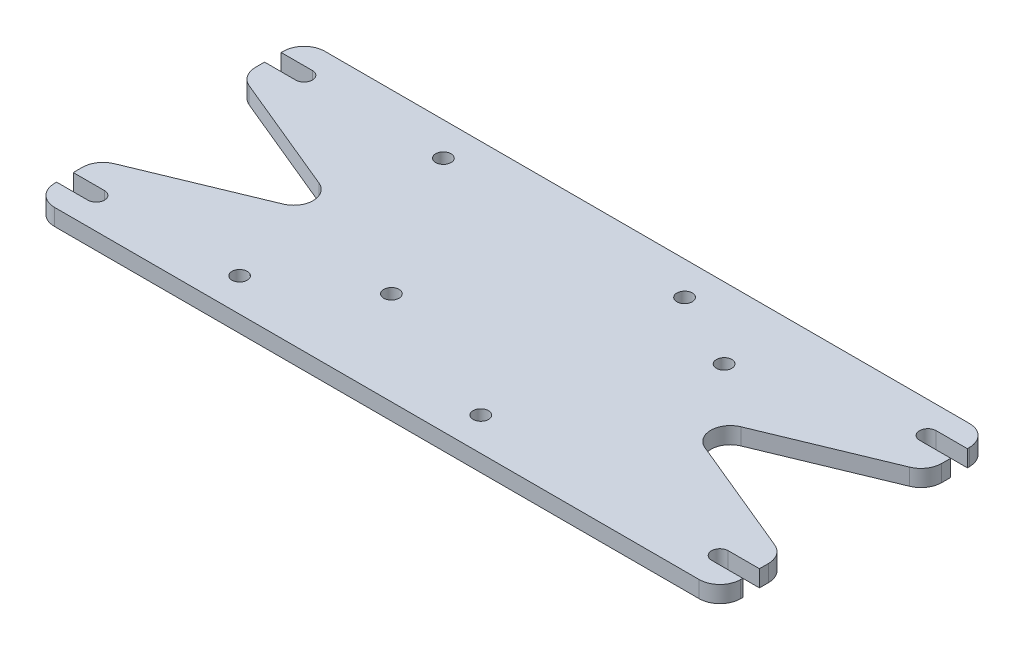
SolidWorks part; units mm, degrees
ref_plane "Alzado" through (0, 0, 0) normal (0, 0, 1) x (1, 0, 0)
ref_plane "Planta" through (0, 0, 0) normal (0, 1, 0) x (1, 0, 0)
ref_plane "Vista lateral" through (0, 0, 0) normal (1, 0, 0) x (0, 0, -1)
sketch "Croquis2" plane through (0, 0, -2.54) normal (0, 1, 0) x (-1, 0, 0)
  line L0 (55, 2.54) -> (-55, 2.54) construction
  line L1 (0, 57.54) -> (0, -52.46) construction
  line L2 (-157.5, 62.04) -> (-165, 62.04)
  line L3 (-157.5, 58.04) -> (-165, 58.04)
  line L4 (-157.5, 12.04) -> (-165, 12.04)
  line L5 (-157.5, 8.04) -> (-165, 8.04)
  line L6 (-7.5, 12.04) -> (0, 12.04)
  line L7 (-7.5, 8.04) -> (0, 8.04)
  line L8 (-7.5, 62.04) -> (0, 62.04)
  line L9 (-7.5, 58.04) -> (0, 58.04)
  line L10 (0, 58.04) -> (0, 52.54)
  line L11 (0, 8.04) -> (0, 2.54)
  line L12 (-165, 58.04) -> (-165, 52.54)
  line L13 (-165, 8.04) -> (-165, 2.54)
  line L32 (-165, 67.54) -> (0, 67.54)
  line L33 (0, 67.54) -> (0, 62.04)
  line L34 (-165, 67.54) -> (-165, 62.04)
  line L35 (-165, 2.54) -> (0, 2.54)
  line L74 (-31.7938, 39.3706) -> (0, 52.54)
  line L76 (-31.7938, 30.7094) -> (0, 17.54)
  line L77 (0, 17.54) -> (0, 12.04)
  line L78 (-165, 17.54) -> (-133.2062, 30.7094)
  line L80 (-133.2062, 39.3706) -> (-165, 52.54)
  line L81 (-165, 17.54) -> (-165, 12.04)
  arc A0 (-157.5, 58.04) -> (-157.5, 62.04) centre (-157.5, 60.04) ccw
  arc A1 (-157.5, 8.04) -> (-157.5, 12.04) centre (-157.5, 10.04) ccw
  arc A2 (-7.5, 62.04) -> (-7.5, 58.04) centre (-7.5, 60.04) ccw
  arc A3 (-7.5, 12.04) -> (-7.5, 8.04) centre (-7.5, 10.04) ccw
  arc A8 (-31.7938, 30.7094) -> (-31.7938, 39.3706) centre (-30, 35.04) cw
  arc A9 (-133.2062, 30.7094) -> (-133.2062, 39.3706) centre (-135, 35.04) ccw
  dimension "D1" = 4
  dimension "D10" = 30
  dimension "D13" = 30
  dimension "D2" = 150
  dimension "D3" = 50
  dimension "D5" = 7.5
  dimension "D6" = 7.5
  dimension "D7" = 7.5
  dimension "D8" = 65
  dimension "D11" = 15
  dimension "D12" = 15
  dimension "D14" = 15
  dimension "D15" = 15
  dimension "D16" = 45
  dimension "D17" = 45
  dimension "D18" = 32.5
extrude "Saliente-Extruir1" add sketch "Croquis2" along normal blind 4
sketch "Croquis3" plane through (0, 4, 0) normal (0, 1, 0) x (-1, 0, 0)
  line L2 (-123, 60.5) -> (-38, 60.5) construction
  line L3 (-123, 60.5) -> (-123, 4.5) construction
  line L4 (-123, 4.5) -> (-38, 4.5) construction
  line L5 (-38, 60.5) -> (-38, 4.5) construction
  circle A0 centre (-99.5, 57) radius 1.85
  circle A1 centre (-41.5, 57) radius 1.85
  circle A2 centre (-41.5, 8) radius 1.85
  circle A3 centre (-99.5, 8) radius 1.85
  circle A4 centre (-63.5, 42.5) radius 1.85
  circle A5 centre (-118.1, 17.1) radius 1.85
  dimension "D1" = 3.7
  dimension "D2" = 25.5
  dimension "D3" = 56
  dimension "D4" = 85
  dimension "D5" = 38
  dimension "D6" = 18
  dimension "D7" = 4.5
  dimension "D8" = 4.9
  dimension "D9" = 12.6
  dimension "D10" = 3.5
  dimension "D11" = 3.5
  dimension "D12" = 58
  dimension "D13" = 49
extrude "Cortar-Extruir1" cut sketch "Croquis3" against normal through all
fillet "Redondeo1" radius 5 8 edges at (165, 2, 15) (0, 2, 15) (165, 2, 65) (0, 2, 65) (165, 2, 50) (165, 2, 0) (0, 2, 50) (0, 2, 0)
